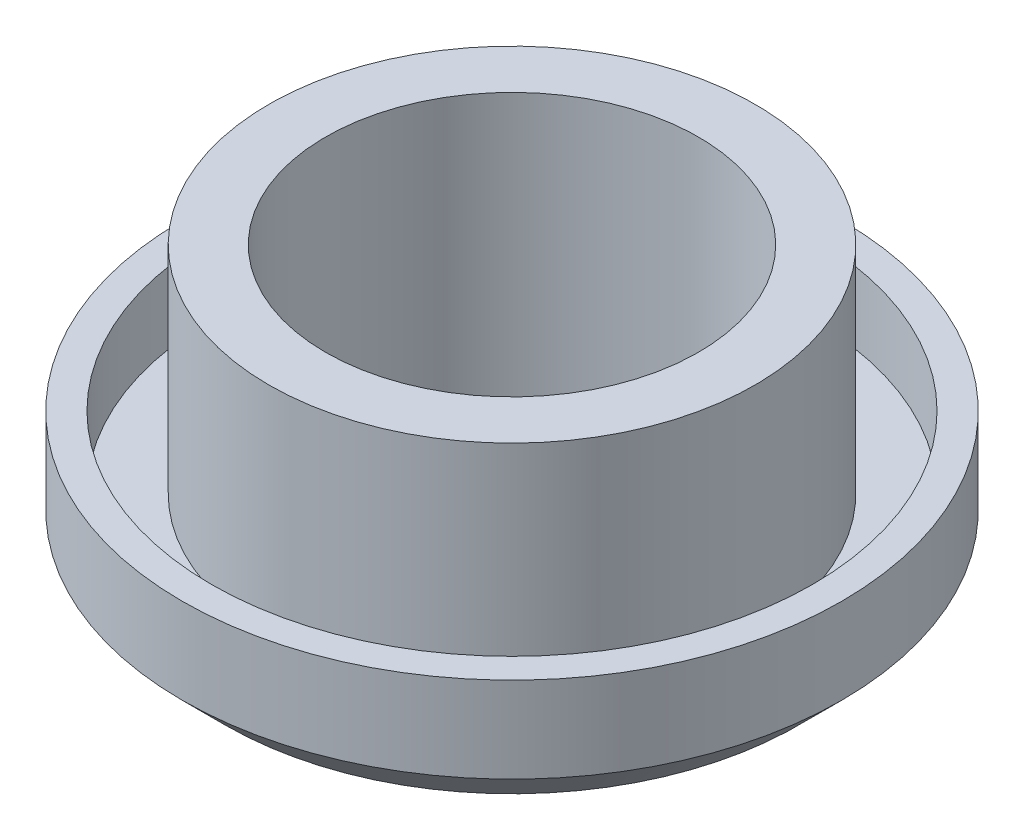
SolidWorks part; units mm, degrees
ref_plane "Front Plane" through (0, 0, 0) normal (0, 0, 1) x (1, 0, 0)
ref_plane "Top Plane" through (0, 0, 0) normal (0, 1, 0) x (1, 0, 0)
ref_plane "Right Plane" through (0, 0, 0) normal (1, 0, 0) x (0, 0, -1)
sketch "Sketch1" plane through (0, 0, 0) normal (0, 0, 1) x (1, 0, 0)
  line L14 (17.6028, 25.472) -> (17.6028, -22.828)
  line L16 (-4.7972, 17.3) -> (-4.7972, -15.5)
  line L17 (-4.7972, -15.5) -> (-21.9972, -15.5)
  line L18 (-21.9972, -15.5) -> (-21.9972, 0)
  line L19 (-21.9972, 0) -> (-18.4972, 0)
  line L20 (-18.4972, 0) -> (-18.4972, -8.6)
  line L21 (-18.4972, -8.6) -> (-11.5972, -8.6)
  line L22 (-11.5972, -8.6) -> (-11.5972, 17.3)
  line L23 (-11.5972, 17.3) -> (-4.7972, 17.3)
  dimension "D1" = 22.4
revolve "Revolve1" add sketch "Sketch1" angle 360 about L14
chamfer "Chamfer1" distance 5.2 angle 45 1 edges at (17.6028, -15.5, 39.6)
